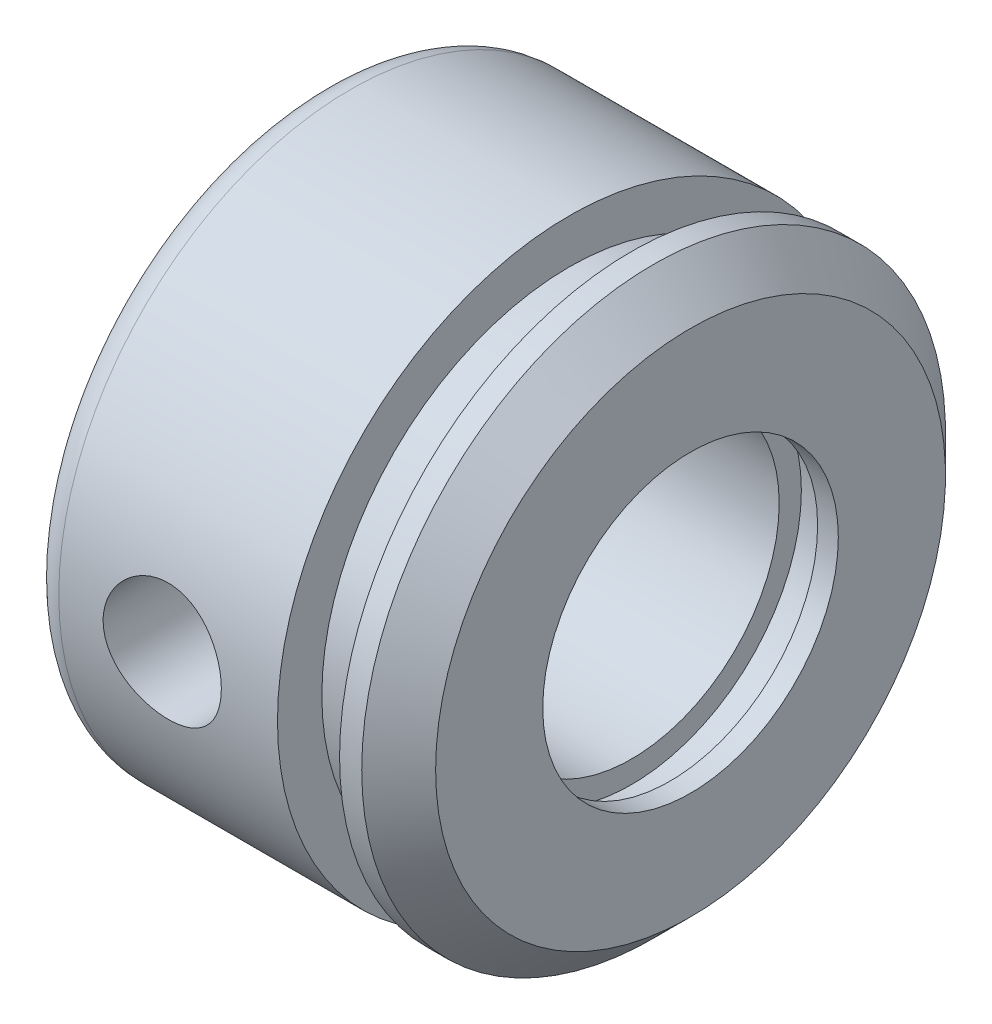
SolidWorks part; units mm, degrees
ref_plane "Plan1" through (0, 0, 0) normal (0, 0, 1) x (1, 0, 0)
ref_plane "Plan2" through (0, 0, 0) normal (0, 1, 0) x (1, 0, 0)
ref_plane "Plan3" through (0, 0, 0) normal (1, 0, 0) x (0, 0, -1)
sketch "Esquisse1" plane through (0, 0, 0) normal (0, 0, 1) x (1, 0, 0)
  line L0 (-92, 0) -> (38, 0) construction
  line L1 (-24, 10) -> (-24, 19.75)
  line L2 (-24, 19.75) -> (-7.2, 19.75)
  line L3 (-7.2, 19.75) -> (-7.2, 16.75)
  line L4 (-7.2, 16.75) -> (-3, 16.75)
  line L5 (-3, 16.75) -> (-3, 19.75)
  line L6 (-3, 19.75) -> (-1.5, 19.75)
  line L7 (-1.5, 19.75) -> (1, 17.25)
  line L8 (1, 17.25) -> (1, 10)
  line L9 (1, 10) -> (-0.4, 10)
  line L10 (-0.4, 10) -> (-0.4, 11.5)
  line L11 (-0.4, 11.5) -> (-3, 11.5)
  line L12 (-3, 11.5) -> (-3, 10)
  line L13 (-3, 10) -> (-24, 10)
  dimension "D1" = 25
  dimension "D2" = 10
  dimension "D3" = 19.75
  dimension "D4" = 1.5
  dimension "D5" = 4.2
  dimension "D6" = 4
  dimension "D7" = 45
  dimension "D8" = 11.5
  dimension "D9" = 1.4
  dimension "D10" = 2.6
revolve "Base-Révolution" add sketch "Esquisse1" angle 360 about L0
sketch "Esquisse2" plane through (0, 0, 0) normal (0, 0, 1) x (1, 0, 0)
  line L0 (-92, 0) -> (38, 0) construction
  line L1 (-24, 19.75) -> (-24, -19.75) construction
  circle A0 centre (-15, 0) radius 4
  dimension "D1" = 8
  dimension "D2" = 9
extrude "Enlèv. mat.-Extru.1" cut sketch "Esquisse2" against normal through all and the other way through all
fillet "Congé2" radius 2
